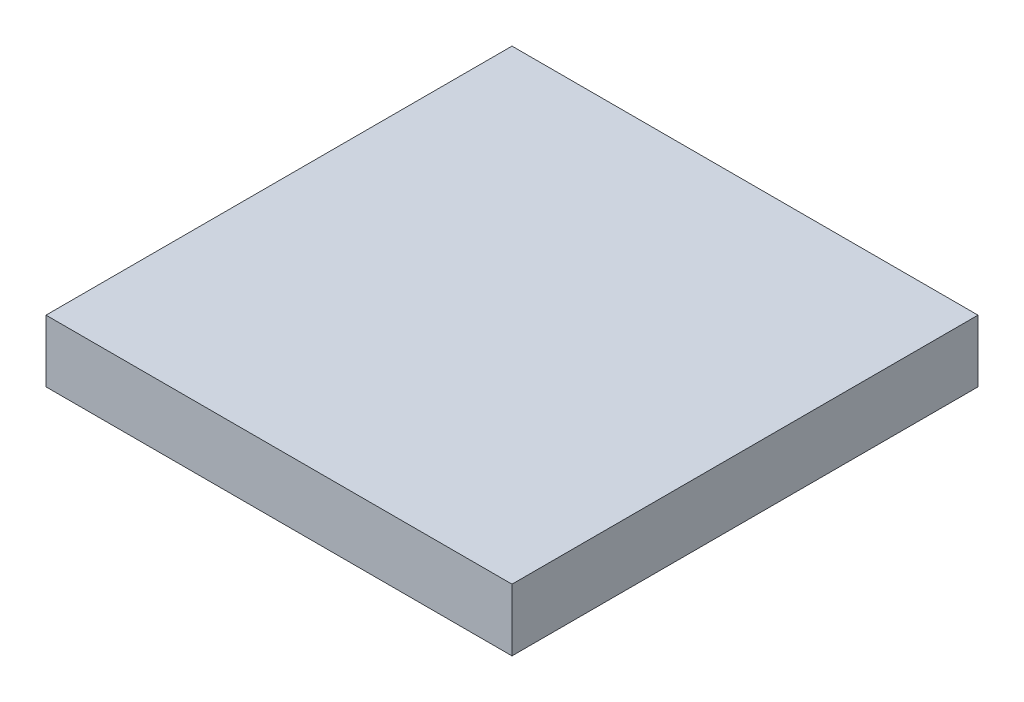
SolidWorks part; units mm, degrees
ref_plane "Front Plane" through (0, 0, 0) normal (0, 0, 1) x (1, 0, 0)
ref_plane "Top Plane" through (0, 0, 0) normal (0, 1, 0) x (1, 0, 0)
ref_plane "Right Plane" through (0, 0, 0) normal (1, 0, 0) x (0, 0, -1)
sketch "Sketch1" plane through (0, 0, 0) normal (0, 1, 0) x (1, 0, 0)
  line L1 (0, 0) -> (15, 0)
  line L2 (0, 0) -> (0, 15)
  line L3 (0, 15) -> (15, 15)
  line L4 (15, 0) -> (15, 15)
  line L5 (0, 0) -> (15, 15) construction
  line L6 (0, 15) -> (15, 0) construction
  point P4 (7.5, 7.5)
  dimension "D1" = 15
  dimension "D2" = 15
extrude "Boss-Extrude1" add sketch "Sketch1" along normal blind 2
